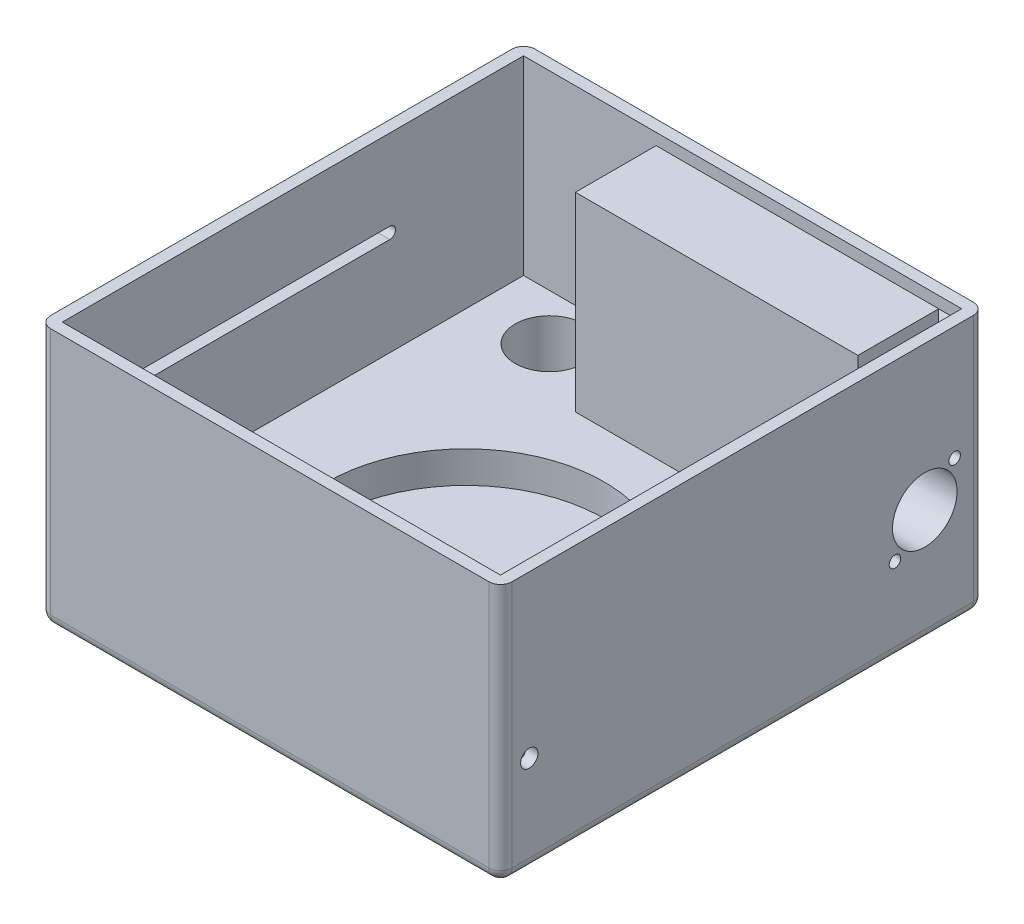
SolidWorks part; units mm, degrees
ref_plane "Front Plane" through (0, 0, 0) normal (0, 0, 1) x (1, 0, 0)
ref_plane "Top Plane" through (0, 0, 0) normal (0, 1, 0) x (1, 0, 0)
ref_plane "Right Plane" through (0, 0, 0) normal (1, 0, 0) x (0, 0, -1)
sketch "Sketch1" plane through (0, 0, 0) normal (0, 1, 0) x (1, 0, 0)
  line L1 (-40, -34) -> (40, -34)
  line L2 (-40, -34) -> (-40, 34)
  line L3 (-40, 34) -> (40, 34)
  line L4 (40, -34) -> (40, 34)
  line L5 (-40, -34) -> (40, 34) construction
  line L6 (-40, 34) -> (40, -34) construction
  point P0 (0, 0)
  dimension "D1" = 80
extrude "Boss-Extrude1" add sketch "Sketch1" along normal blind 45
sketch "Sketch2" plane through (0, 0, 0) normal (0, 1, 0) x (1, 0, 0)
  line L1 (-38, -32) -> (38, -32)
  line L2 (-38, -32) -> (-38, 32)
  line L3 (-38, 32) -> (38, 32)
  line L4 (38, -32) -> (38, 32)
  line L5 (-38, -32) -> (38, 32) construction
  line L6 (-38, 32) -> (38, -32) construction
  point P0 (0, 0)
  dimension "D1" = 76
extrude "Cut-Extrude1" cut sketch "Sketch2" against normal blind 33 from surface at 45 starting at face at (0, 45, 0)
sketch "Sketch5" plane through (0, 0, 0) normal (0, 1, 0) x (1, 0, 0)
  circle A0 centre (0, 0) radius 5.95
  dimension "D1" = 11.9
sketch "Sketch6" plane through (0, 0, 0) normal (0, -1, 0) x (1, 0, 0)
  circle A0 centre (0, 0) radius 10.5
  dimension "D1" = 21
extrude "Cut-Extrude10" cut sketch "Sketch6" against normal blind 5 from surface at 0 starting at face at (0, 0, 0)
sketch "Sketch7" plane through (0, 0, 0) normal (0, -1, 0) x (-1, 0, 0)
  line L0 (-34, 34) -> (34, -34) construction
  line L1 (-34, -34) -> (34, 34) construction
  line L3 (-15, 15) -> (15, 15)
  line L4 (-15, 15) -> (-15, -15)
  line L5 (-15, -15) -> (15, -15)
  line L6 (15, 15) -> (15, -15)
  line L7 (-13, 13) -> (13, 13)
  line L8 (-13, 13) -> (-13, -13)
  line L9 (-13, -13) -> (13, -13)
  line L10 (13, 13) -> (13, -13)
  point P8 (0, 0)
  dimension "D1" = 30
  dimension "D2" = 26
extrude "Cut-Extrude11" cut sketch "Sketch7" against normal blind 2
sketch "Sketch8" plane through (38, 0, 0) normal (-1, 0, 0) x (0, 0, 1)
  line L0 (32, 12) -> (-32, 12) construction
  line L2 (32, 12) -> (32, 45) construction
  circle A0 centre (29, 17) radius 1.5
  dimension "D1" = 3
  dimension "D2" = 5
  dimension "D3" = 3
extrude "Cut-Extrude12" cut sketch "Sketch8" against normal through all
extrude "Cut-Extrude14" cut sketch "Sketch5" along normal through all
fillet "Fillet1" radius 0.5 8 edges at (0, 0, 13) (13, 0, 0) (0, 0, -13) (-13, 0, 0) (0, 0, 15) (15, 0, 0) (0, 0, -15) (-15, 0, 0)
sketch "Sketch12" plane through (0, 0, 0) normal (0, 1, 0) x (1, 0, 0)
  circle A0 centre (0, 0) radius 24
  dimension "D1" = 48
extrude "Cut-Extrude15" cut sketch "Sketch12" against normal blind 5.5 from surface at 12 starting at face at (0, 12, 5.95)
sketch "Sketch13" plane through (0, 0, 0) normal (0, 0, 1) x (1, 0, 0)
  line L1 (-40, 45) -> (40, 45)
  line L2 (-40, 45) -> (-40, 0)
  line L3 (-40, 0) -> (40, 0)
  line L4 (40, 45) -> (40, 0)
extrude "Boss-Extrude5" add sketch "Sketch13" against normal blind 16 from surface at -34 starting at face at (0, 22.5, -34)
sketch "Sketch15" plane through (0, 0, 0) normal (0, 1, 0) x (1, 0, 0)
  line L0 (40, 50) -> (-40, 50) construction
  line L1 (-38, 32) -> (-13, 32)
  line L2 (-38, 32) -> (-38, 48)
  line L3 (-38, 48) -> (-13, 48)
  line L4 (-13, 32) -> (-13, 48)
  dimension "D1" = 25
  dimension "D2" = 2
extrude "Cut-Extrude16" cut sketch "Sketch15" against normal blind 33 from surface at 45 starting at face at (0, 45, 0)
sketch "Sketch16" plane through (0, 12, 0) normal (0, 1, 0) x (1, 0, 0)
  line L0 (-38, 48) -> (-13, 32) construction
  line L1 (-38, 32) -> (-13, 48) construction
  line L2 (-38, 48) -> (-38, -32) construction
  circle A0 centre (-25.5, 40) radius 5.95
  dimension "D1" = 11.9
extrude "Cut-Extrude17" cut sketch "Sketch16" against normal blind 10 from surface at 0 starting at face at (0, 12, 24)
sketch "Sketch17" plane through (0, 0, 0) normal (1, 0, 0) x (0, 0, -1)
  line L1 (32, 12) -> (32, 45) construction
  line L2 (-34, 0) -> (50, 0) construction
  circle A0 centre (39.6, 20.0023) radius 5.6
  dimension "D1" = 11.2
  dimension "D2" = 7.6
  dimension "D3" = 20.0023
extrude "Cut-Extrude18" cut sketch "Sketch17" against normal blind 50 from surface at 40 starting at face at (40, 17, 30.5)
sketch "Sketch20" plane through (0, 0, 0) normal (1, 0, 0) x (0, 0, -1)
  line L1 (34.425, 14.8273) -> (44.775, 14.8273) construction
  line L2 (34.425, 14.8273) -> (34.425, 25.1773) construction
  line L3 (34.425, 25.1773) -> (44.775, 25.1773) construction
  line L4 (44.775, 14.8273) -> (44.775, 25.1773) construction
  line L5 (34.425, 14.8273) -> (44.775, 25.1773) construction
  line L6 (34.425, 25.1773) -> (44.775, 14.8273) construction
  circle A2 centre (44.775, 25.1773) radius 1
  circle A3 centre (34.425, 14.8273) radius 1
  point P0 (39.6, 20.0023)
  dimension "D3" = 2
  dimension "D4" = 2
  dimension "D1" = 10.35
  dimension "D2" = 10.35
extrude "Cut-Extrude19" cut sketch "Sketch20" against normal up to next (13 mm away) from surface at 40 starting at face at (40, 20.0023, -34)
fillet "Fillet3" radius 2 4 edges at (40, 22.5, 34) (40, 22.5, -50) (-40, 22.5, -50) (-40, 22.5, 34)
fillet "Fillet4" radius 2 8 edges at (-39.4142, 0, -49.4142) (39.4142, 0, -49.4142) (39.4142, 0, 33.4142) (-39.4142, 0, 33.4142) (0, 0, 34) (40, 0, -8) (0, 0, -50) (-40, 0, -8)
sketch "Sketch21" plane through (0, 0, 0) normal (0, 1, 0) x (1, 0, 0)
  line L0 (40, -32) -> (40, 48) construction
  line L1 (-13, 48) -> (38, 48)
  line L2 (-13, 48) -> (-13, 46)
  line L3 (-13, 46) -> (38, 46)
  line L4 (38, 48) -> (38, 46)
  point P7 (38, 47)
  dimension "D1" = 2
  dimension "D2" = 2
extrude "Cut-Extrude20" cut sketch "Sketch21" against normal blind 2 from surface at 45 starting at face at (-4.3333, 45, -16)
sketch "Sketch22" plane through (0, 0, 0) normal (0, 1, 0) x (1, 0, 0)
  line L0 (38, 32) -> (-13, 32) construction
  line L1 (38, 46) -> (36, 46)
  line L2 (38, 46) -> (38, 32)
  line L3 (38, 32) -> (36, 32)
  line L4 (36, 46) -> (36, 32)
  dimension "D1" = 2
extrude "Cut-Extrude22" cut sketch "Sketch22" against normal blind 2 from surface at 45 starting at face at (6.25, 45, -23.5)
sketch "Sketch23" plane through (0, 0, 0) normal (1, 0, 0) x (0, 0, -1)
  line L0 (-20.2059, 30) -> (24.7941, 30) construction
  line L1 (-20.2059, 31) -> (24.7941, 31)
  line L2 (-20.2059, 29) -> (24.7941, 29)
  line L3 (48, 45) -> (-32, 45) construction
  arc A0 (-20.2059, 31) -> (-20.2059, 29) centre (-20.2059, 30) ccw
  arc A1 (24.7941, 29) -> (24.7941, 31) centre (24.7941, 30) ccw
  point P2 (2.2941, 30)
  dimension "D1" = 2
  dimension "D2" = 15
  dimension "D3" = 45
extrude "Cut-Extrude23" cut sketch "Sketch23" along normal blind 2 from surface at -40 starting at face at (-40, 23.5, -8)
